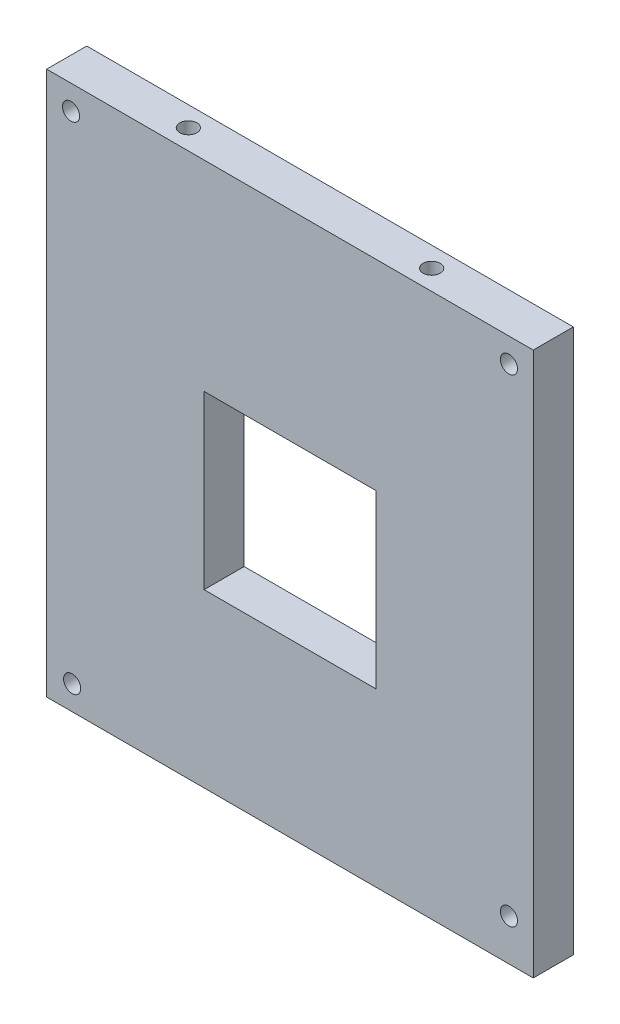
SolidWorks part; units mm, degrees
ref_plane "Front Plane" through (0, 0, 0) normal (0, 0, 1) x (1, 0, 0)
ref_plane "Top Plane" through (0, 0, 0) normal (0, 1, 0) x (1, 0, 0)
ref_plane "Right Plane" through (0, 0, 0) normal (1, 0, 0) x (0, 0, -1)
sketch "Sketch1" plane through (0, 0, 0) normal (0, 0, 1) x (1, 0, 0)
  line L1 (0, 0) -> (85, 0)
  line L2 (0, 0) -> (0, 95)
  line L3 (0, 95) -> (85, 95)
  line L4 (85, 0) -> (85, 95)
  dimension "D1" = 95
  dimension "D2" = 85
extrude "Boss-Extrude1" add sketch "Sketch1" along normal blind 7
sketch "Sketch2" plane through (0, 0, 7) normal (0, 0, 1) x (1, 0, 0)
  line L0 (0, 0) -> (85, 0) construction
  line L1 (27.5, 30) -> (57.5, 30)
  line L2 (27.5, 30) -> (27.5, 60)
  line L3 (27.5, 60) -> (57.5, 60)
  line L4 (57.5, 30) -> (57.5, 60)
  line L5 (27.5, 30) -> (57.5, 60) construction
  line L6 (27.5, 60) -> (57.5, 30) construction
  point P0 (42.5, 45)
  point P7 (42.5, 0)
  dimension "D1" = 0
  dimension "D2" = 30
  dimension "D3" = 30
  dimension "D4" = 45
extrude "Cut-Extrude1" cut sketch "Sketch2" against normal blind 7
sketch "Sketch4" plane through (0, 95, 0) normal (0, 1, 0) x (1, 0, 0)
  line L0 (0, -3.5) -> (85, -3.5) construction
  line L1 (0, -7) -> (0, 0) construction
  line L2 (85, -7) -> (85, 0) construction
  circle A0 centre (21.25, -3.5) radius 1.5
  circle A1 centre (63.75, -3.5) radius 1.5
  dimension "D1" = 3
  dimension "D2" = 3
  dimension "D3" = 21.25
  dimension "D4" = 21.25
extrude "Cut-Extrude2" cut sketch "Sketch4" against normal blind 5
sketch "Sketch6" plane through (0, 0, 0) normal (0, 0, -1) x (-1, 0, 0)
  line L0 (-85, 95) -> (0, 95) construction
  line L1 (-85, 0) -> (-85, 95) construction
  line L2 (-42.5, 60) -> (-42.5, 65.8033) construction
  line L3 (-57.5, 60) -> (-27.5, 60) construction
  line L4 (0, 95) -> (0, 0) construction
  line L5 (0, 0) -> (-85, 0) construction
  circle A0 centre (-80.75, 90.75) radius 1.5
  circle A1 centre (-4.25, 90.75) radius 1.5
  circle A2 centre (-4.45, 4.25) radius 1.5
  circle A3 centre (-80.75, 7.25) radius 1.5
  dimension "D1" = 3
  dimension "D5" = 3
  dimension "D7" = 3
  dimension "D2" = 4.25
  dimension "D3" = 4.25
  dimension "D4" = 4.45
  dimension "D6" = 4.25
  dimension "D8" = 7.25
  dimension "D9" = 4.25
extrude "Cut-Extrude3" cut sketch "Sketch6" against normal blind 8
